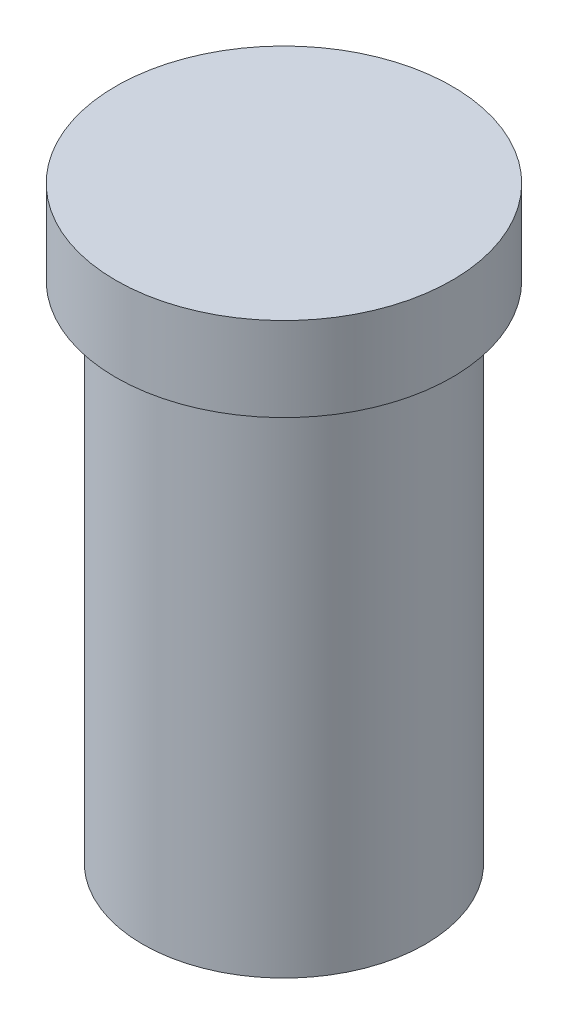
SolidWorks part; units mm, degrees
ref_plane "Front Plane" through (0, 0, 0) normal (0, 0, 1) x (1, 0, 0)
ref_plane "Top Plane" through (0, 0, 0) normal (0, 1, 0) x (1, 0, 0)
ref_plane "Right Plane" through (0, 0, 0) normal (1, 0, 0) x (0, 0, -1)
sketch "Sketch1" plane through (0, 0, 0) normal (0, 0, 1) x (1, 0, 0)
  line L0 (-3.175, -18.415) -> (-3.175, -22.225)
  line L1 (-3.175, -22.225) -> (-5.334, -22.225)
  line L2 (-5.334, -22.225) -> (-5.334, -3.175)
  line L3 (-5.334, -3.175) -> (-6.35, -3.175)
  line L4 (-6.35, -3.175) -> (-6.35, 0)
  line L5 (-6.35, 0) -> (0, 0)
  line L6 (0, 0) -> (0, -7.0255) construction
  line L7 (-3.175, -18.415) -> (0, -18.415)
  line L8 (0, -18.415) -> (0, 0)
  dimension "D1" = 3.175
  dimension "D2" = 5.334
  dimension "D3" = 3.175
  dimension "D4" = 6.35
  dimension "D5" = 22.225
  dimension "D6" = 18.415
revolve "Revolve1" add sketch "Sketch1" angle 360 about L6
